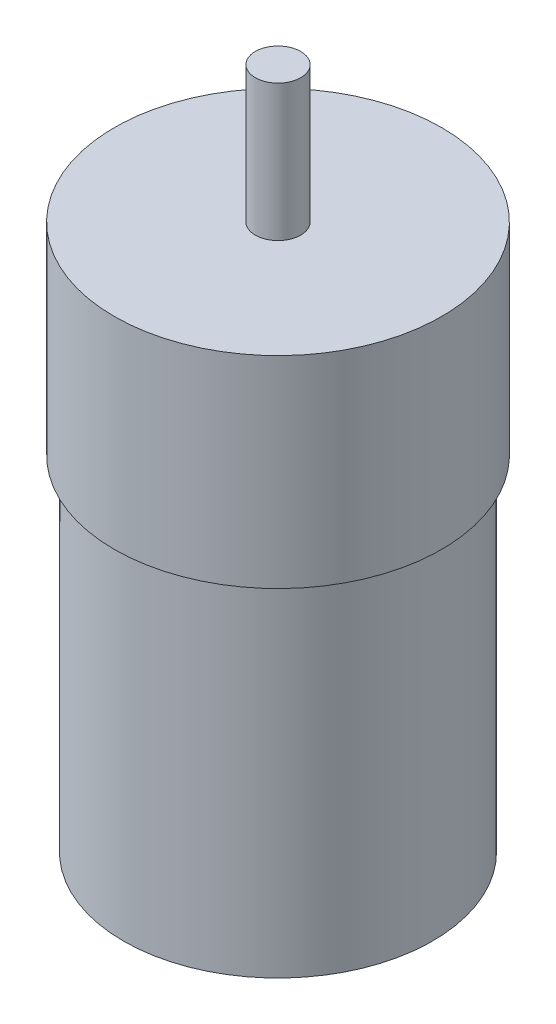
SolidWorks part; units mm, degrees
ref_plane "Front Plane" through (0, 0, 0) normal (0, 0, 1) x (1, 0, 0)
ref_plane "Top Plane" through (0, 0, 0) normal (0, 1, 0) x (1, 0, 0)
ref_plane "Right Plane" through (0, 0, 0) normal (1, 0, 0) x (0, 0, -1)
sketch "Sketch2" plane through (0, 0, 0) normal (0, 0, 1) x (1, 0, 0)
  line L0 (0, 0) -> (0, -60)
  line L1 (0, -60) -> (17, -60)
  line L2 (17, -60) -> (17, -22.1918)
  line L3 (17, -22.1918) -> (18, -22.1918)
  line L4 (18, -22.1918) -> (18, 0)
  line L5 (18, 0) -> (2.5, 0)
  line L6 (2.5, 0) -> (2.5, 15)
  line L7 (2.5, 15) -> (0, 15)
  line L8 (0, 15) -> (0, 0)
  line L9 (0, 0) -> (-0.345, 0.0995)
  line L10 (0, 55.3822) -> (0, -96.9292) construction
  dimension "D1" = 60
  dimension "D2" = 18
  dimension "D3" = 17
  dimension "D4" = 2.5
  dimension "D5" = 15
revolve "Revolve2" add sketch "Sketch2" angle 360 about L10
